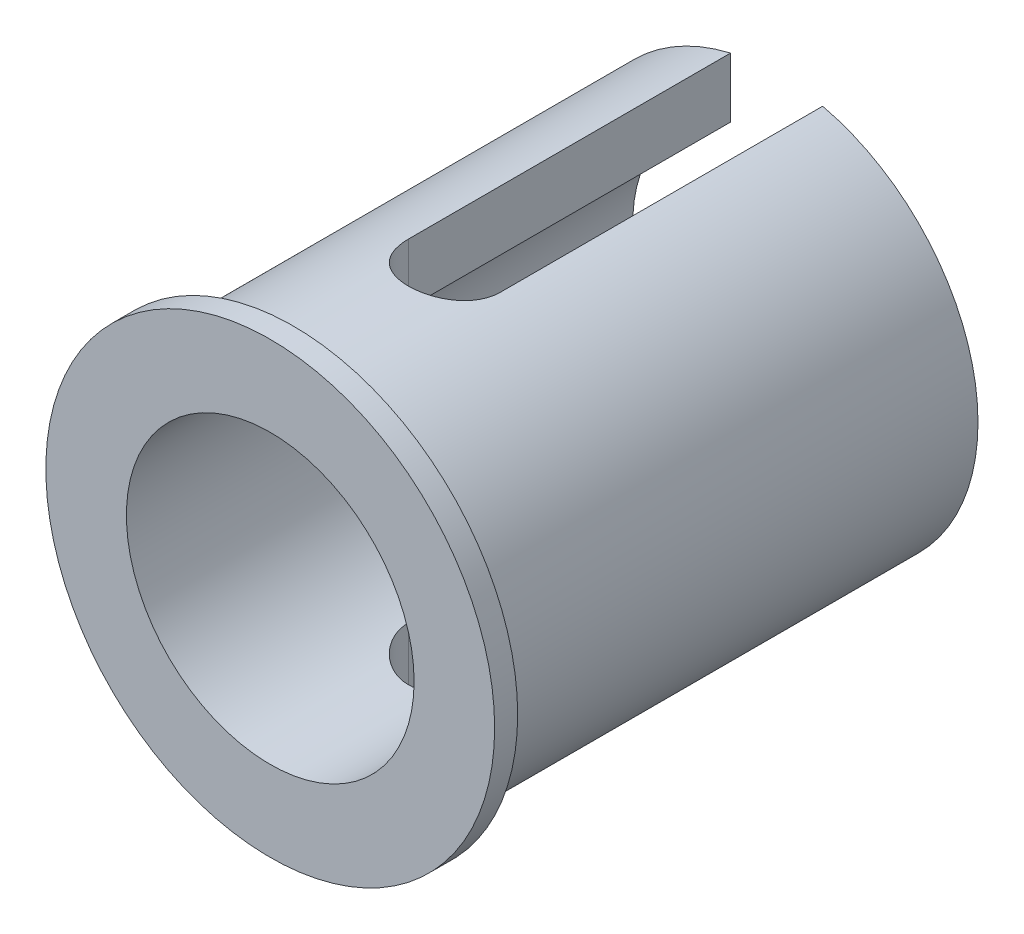
SolidWorks part; units mm, degrees
material "AISI 1020"
ref_plane "Спереди" through (0, 0, 0) normal (0, 0, 1) x (1, 0, 0)
ref_plane "Сверху" through (0, 0, 0) normal (0, 1, 0) x (1, 0, 0)
ref_plane "Справа" through (0, 0, 0) normal (1, 0, 0) x (0, 0, -1)
sketch "Эскиз1" plane through (0, 0, 0) normal (0, 0, 1) x (1, 0, 0)
  circle A1 centre (0, 0) radius 17.5
  circle A2 centre (0, 0) radius 12.5
  circle A3 centre (0, 0) radius 17.5 construction
  dimension "D1" = 25
  dimension "D2" = 35
extrude "Бобышка-Вытянуть1" add sketch "Эскиз1" along normal blind 2 and the other way offset from surface (42 mm away) 15 contours A1 A2
sketch "Эскиз2" plane through (0, 0, 2) normal (0, 0, 1) x (1, 0, 0)
  circle A0 centre (0, 0) radius 17.5 construction
  circle A1 centre (0, 0) radius 17.5
  circle A2 centre (0, 0) radius 19.5
  dimension "D1" = 2
extrude "Бобышка-Вытянуть2" add sketch "Эскиз2" against normal up to surface (2 mm away) contours A1 | A2
sketch "Эскиз3" plane through (0, 0, 0) normal (0, 1, 0) x (1, 0, 0)
  line L0 (0, 42) -> (0, 14) construction
  line L1 (4, 42) -> (4, 14)
  line L2 (-4, 42) -> (-4, 14)
  line L3 (12.5, 42) -> (-12.5, 42) construction
  line L4 (19.5, 0) -> (-19.5, 0) construction
  arc A0 (4, 42) -> (-4, 42) centre (0, 42) ccw
  arc A1 (-4, 14) -> (4, 14) centre (0, 14) ccw
  point P3 (0, 28)
  dimension "D1" = 10
  dimension "D2" = 8
extrude "Вырез-Вытянуть1" cut sketch "Эскиз3" against normal through all both and the other way through all contours L1 A1 L2 A0
